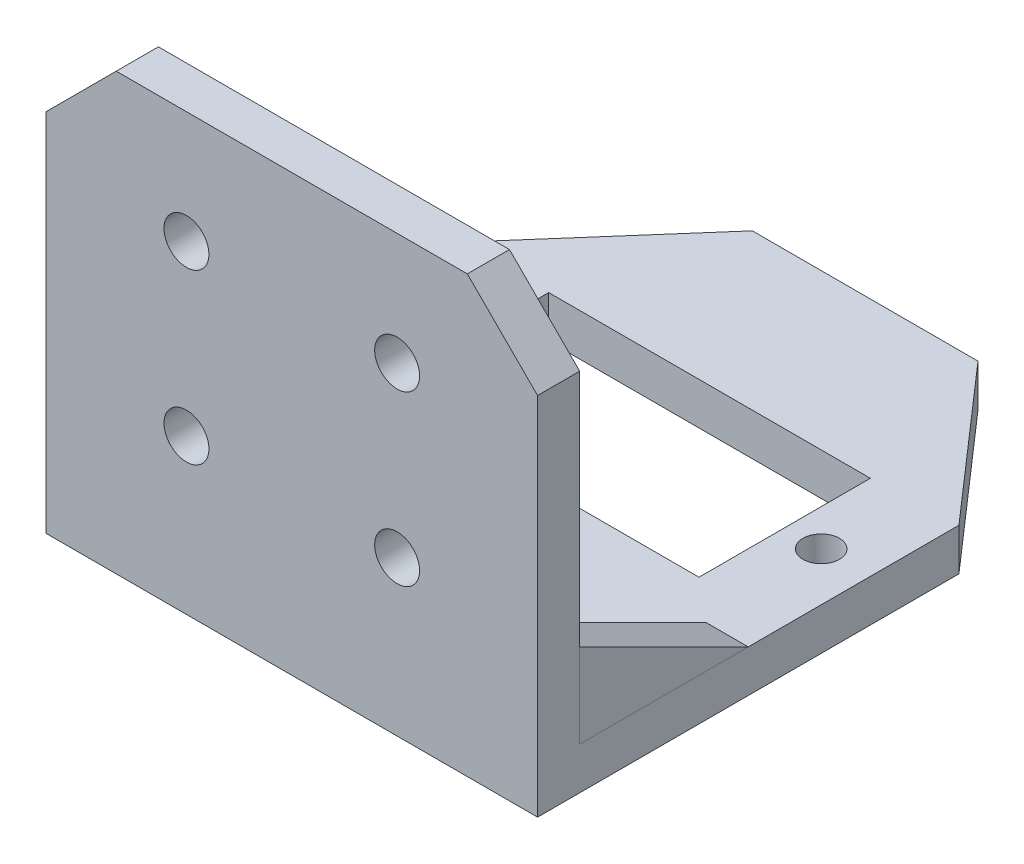
SolidWorks part; units mm, degrees
material "PLA"
ref_plane "Front Plane" through (0, 0, 0) normal (0, 0, 1) x (1, 0, 0)
ref_plane "Top Plane" through (0, 0, 0) normal (0, 1, 0) x (1, 0, 0)
ref_plane "Right Plane" through (0, 0, 0) normal (1, 0, 0) x (0, 0, -1)
sketch "Sketch2" plane through (0, 0, 0) normal (0, 1, 0) x (1, 0, 0)
  line L3 (-15.2811, -78.6746) -> (-50.2811, -78.6746)
  line L5 (-50.2306, -48.6747) -> (-50.2811, -78.6746)
  line L6 (-50.2306, -48.6747) -> (-40.7895, -37.8746)
  line L7 (-24.7222, -37.8746) -> (-40.7895, -37.8746)
  line L8 (-15.2811, -48.6746) -> (-15.2811, -78.6746)
  line L9 (-24.7222, -37.8746) -> (-15.2811, -48.6746)
  line L11 (-21.3311, -48.9306) -> (-44.2311, -48.9306)
  line L12 (-21.3311, -48.9306) -> (-21.3311, -61.1306)
  line L13 (-21.3311, -61.1306) -> (-44.2311, -61.1306)
  line L14 (-44.2311, -48.9306) -> (-44.2311, -61.1306)
  circle A0 centre (-46.7311, -55.0306) radius 1.3
  circle A1 centre (-18.7311, -55.0306) radius 1.3
  point P0 (-32.7558, -37.8746)
  dimension "D3" = 6.05
  dimension "D4" = 28
  dimension "D6" = 11.056
  dimension "D1" = 35
  dimension "D2" = 10.8
  dimension "D5" = 2.5
  dimension "D9" = 30
extrude "Boss-Extrude1" add sketch "Sketch2" along normal blind 3
sketch "Sketch4" plane through (0, 3, 0) normal (0, 1, 0) x (1, 0, 0)
  line L0 (-15.2811, -78.6746) -> (-15.2811, -48.6746) construction
  line L1 (-50.2811, -78.6746) -> (-15.2811, -78.6746)
  line L2 (-50.2811, -78.6746) -> (-50.2811, -75.6746)
  line L3 (-50.2811, -75.6746) -> (-15.2811, -75.6746)
  line L4 (-15.2811, -78.6746) -> (-15.2811, -75.6746)
extrude "Boss-Extrude2" add sketch "Sketch4" along normal blind 28
sketch "Sketch5" plane through (0, 0, 75.6746) normal (0, 0, -1) x (-1, 0, 0)
  line L0 (15.2811, 31) -> (15.2811, 26)
  line L1 (15.2811, 31) -> (15.2811, 3) construction
  line L2 (15.2811, 26) -> (20.2811, 31)
  line L3 (15.2811, 31) -> (50.2811, 31) construction
  line L4 (20.2811, 31) -> (15.2811, 31)
  line L5 (50.2811, 31) -> (45.2811, 31)
  line L6 (45.2811, 31) -> (50.2811, 26)
  line L7 (50.2811, 31) -> (50.2811, 3) construction
  line L8 (50.2811, 26) -> (50.2811, 31)
  dimension "D1" = 5
  dimension "D2" = 5
  dimension "D3" = 5
  dimension "D4" = 5
extrude "Cut-Extrude1" cut sketch "Sketch5" against normal blind 8
hole_wizard "Ø3.2 (3.2) Diameter Hole1" positions "Sketch8" profile "Sketch9" hole size "Ø3.2" standard "ANSI Metric"
sketch "Sketch8" plane through (0, 0, 75.6746) normal (0, 0, -1) x (-1, 0, 0)
  line L0 (20.2811, 31) -> (45.2811, 31) construction
  line L1 (15.2811, 3) -> (50.276, 3) construction
  line L2 (50.2811, 26) -> (50.2811, 3) construction
  line L3 (50.2811, 26) -> (50.2811, 3) construction
  line L4 (15.2811, 26) -> (15.2811, 3) construction
  point P0 (25.2811, 23)
  point P2 (40.2811, 23)
  point P4 (40.2811, 11)
  point P6 (25.2811, 11)
  point P19 (7.4303, 12.3175)
  dimension "D1" = 8
  dimension "D2" = 8
  dimension "D3" = 8
  dimension "D4" = 8
  dimension "D5" = 10
  dimension "D6" = 10
  dimension "D7" = 10
  dimension "D8" = 10
sketch "Sketch9" plane through (-25.2811, 23, 75.6746) normal (1, 0, 0) x (0, 1, 0)
  line L0 (0, 0) -> (0, 4.1614)
  line L1 (0, 4.1614) -> (1.6, 3.2)
  line L2 (1.6, 3.2) -> (1.6, 0)
  line L5 (1.6, 0) -> (0, 0)
  line L10 (0, 4.1614) -> (-1.6, 3.2) construction
  line L11 (0, -6.35) -> (0, 107.95) construction
  dimension "Hole Dia." = 3.2
  dimension "Hole Depth" = 3.2
  dimension "Drill Angle" = 118
other "Gusset1" parameters "D1"=3, "D2"=3, "D3"=0, "D4"=0, "D10"=5, "D11"=12, "D12"=6, "D13"=15, "D14"=45, "D15"=15, "D16"=5, "D17"=5, "D18"=45
sketch "Sketch10" plane through (-50.276, 3, 75.6746) normal (1, 0, 0) x (0, 0, -1)
  line L0 (0, 0) -> (12, 0)
  line L1 (0, 0) -> (0, 6)
  line L2 (12, 0) -> (0, 6)
other "Gusset2" parameters "D1"=3, "D2"=3, "D3"=0, "D4"=0, "D10"=5, "D11"=6, "D12"=12, "D13"=15, "D14"=45, "D15"=15, "D16"=5, "D17"=5, "D18"=45
sketch "Sketch11" plane through (-15.2811, 3, 75.6746) normal (-1, 0, 0) x (0, 0, 1)
  line L0 (0, 0) -> (0, 6)
  line L1 (0, 0) -> (-12, 0)
  line L2 (0, 6) -> (-12, 0)
